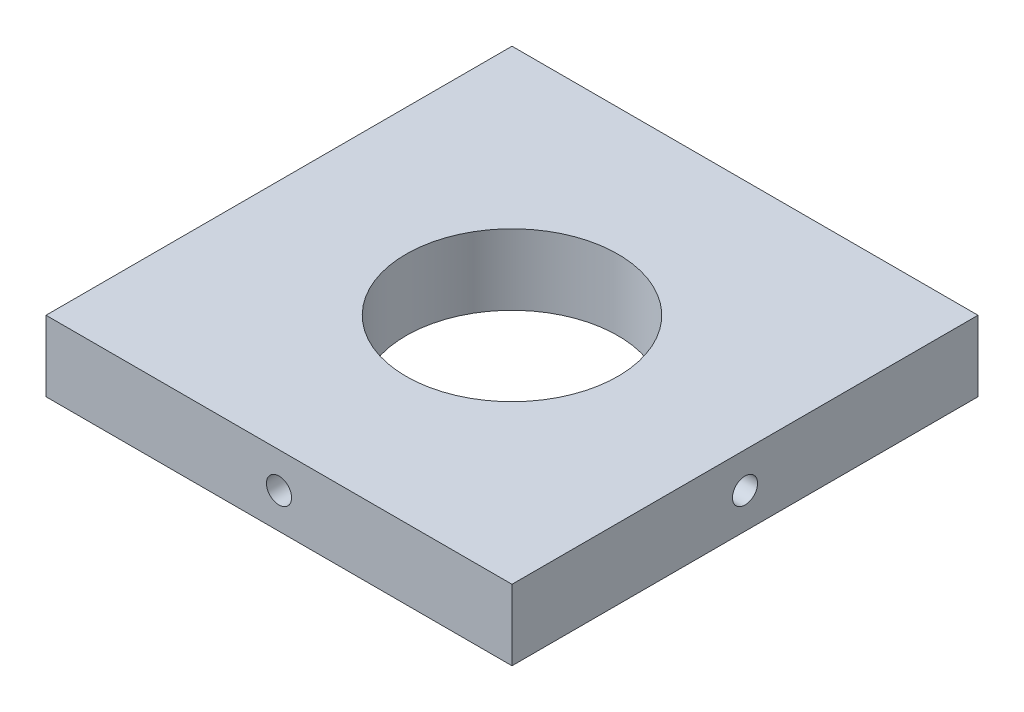
SolidWorks part; units mm, degrees
ref_plane "Front Plane" through (0, 0, 0) normal (0, 0, 1) x (1, 0, 0)
ref_plane "Top Plane" through (0, 0, 0) normal (0, 1, 0) x (1, 0, 0)
ref_plane "Right Plane" through (0, 0, 0) normal (1, 0, 0) x (0, 0, -1)
sketch "Sketch1" plane through (0, 0, 0) normal (0, 1, 0) x (1, 0, 0)
  line L1 (-16.5, -16.5) -> (16.5, -16.5)
  line L2 (-16.5, -16.5) -> (-16.5, 16.5)
  line L3 (-16.5, 16.5) -> (16.5, 16.5)
  line L4 (16.5, -16.5) -> (16.5, 16.5)
  circle A0 centre (0, 0) radius 7.5
extrude "Boss-Extrude1" add sketch "Sketch1" along normal blind 5
sketch "Sketch2" plane through (0, 0, 16.5) normal (0, 0, 1) x (1, 0, 0)
  line L0 (-16.5, 5) -> (16.5, 0)
  line L1 (-16.5, 0) -> (16.5, 5)
  point P8 (0, 0)
hole_wizard "#2-56 Tapped Hole4" positions "Sketch14" profile "Sketch15" tap size "#2-56" standard "ANSI Inch"
sketch "Sketch14" plane through (0, 0, 16.5) normal (0, 0, 1) x (1, 0, 0)
  line L0 (-16.5, 5) -> (16.5, 0) construction
  point P0 (0, 2.5)
sketch "Sketch15" plane through (0, 2.5, 16.5) normal (1, 0, 0) x (0, -1, 0)
  line L0 (0, 0) -> (0, 7)
  line L1 (0, 7) -> (0.889, 6.4658)
  line L2 (0.889, 6.4658) -> (0.889, 0)
  line L5 (0.889, 0) -> (0, 0)
  line L10 (0, 7) -> (-0.889, 6.4658) construction
  line L11 (0, -6.35) -> (0, 107.95) construction
  dimension "Tap Drill Dia." = 1.778
  dimension "Tap Drill Depth" = 7
  dimension "Drill Angle" = 118
cosmetic thread "Hole Thread4"
sketch "Sketch18" plane through (0, 0, -16.5) normal (0, 0, -1) x (-1, 0, 0)
  line L0 (-16.5, 5) -> (16.5, 0)
  line L1 (-16.5, 0) -> (16.5, 5)
hole_wizard "#2-56 Tapped Hole5" positions "Sketch19" profile "Sketch20" tap size "#2-56" standard "ANSI Inch"
sketch "Sketch19" plane through (0, 0, -16.5) normal (0, 0, -1) x (-1, 0, 0)
  line L0 (16.5, 5) -> (-16.5, 0) construction
  point P0 (0, 2.5)
sketch "Sketch20" plane through (0, 2.5, -16.5) normal (1, 0, 0) x (0, 1, 0)
  line L0 (0, 0) -> (0, 8)
  line L1 (0, 8) -> (0.889, 7.4658)
  line L2 (0.889, 7.4658) -> (0.889, 0)
  line L5 (0.889, 0) -> (0, 0)
  line L10 (0, 8) -> (-0.889, 7.4658) construction
  line L11 (0, -6.35) -> (0, 107.95) construction
  dimension "Tap Drill Dia." = 1.778
  dimension "Tap Drill Depth" = 8
  dimension "Drill Angle" = 118
cosmetic thread "Hole Thread5"
sketch "Sketch21" plane through (16.5, 0, 0) normal (1, 0, 0) x (0, 0, -1)
  line L0 (-16.5, 5) -> (16.5, 0)
  line L1 (16.5, 5) -> (-16.5, 0)
  line L2 (-16.5, 0) -> (-16.5, 5) construction
  line L3 (-16.5, 0) -> (16.5, 0) construction
hole_wizard "#2-56 Tapped Hole6" positions "Sketch22" profile "Sketch23" tap size "#2-56" standard "ANSI Inch"
sketch "Sketch22" plane through (16.5, 0, 0) normal (1, 0, 0) x (0, 0, -1)
  line L0 (-16.5, 5) -> (16.5, 0) construction
  point P0 (0, 2.5)
sketch "Sketch23" plane through (16.5, 2.5, 0) normal (0, 1, 0) x (0, 0, -1)
  line L0 (0, 0) -> (0, 8)
  line L1 (0, 8) -> (0.889, 7.4658)
  line L2 (0.889, 7.4658) -> (0.889, 0)
  line L5 (0.889, 0) -> (0, 0)
  line L10 (0, 8) -> (-0.889, 7.4658) construction
  line L11 (0, -6.35) -> (0, 107.95) construction
  dimension "Tap Drill Dia." = 1.778
  dimension "Tap Drill Depth" = 8
  dimension "Drill Angle" = 118
cosmetic thread "Hole Thread6"
sketch "Sketch24" plane through (-16.5, 0, 0) normal (-1, 0, 0) x (0, 0, 1)
  line L0 (-16.5, 5) -> (16.5, 0)
  line L1 (-16.5, 0) -> (16.5, 5)
hole_wizard "#2-56 Tapped Hole7" positions "Sketch25" profile "Sketch26" tap size "#2-56" standard "ANSI Inch"
sketch "Sketch25" plane through (-16.5, 0, 0) normal (-1, 0, 0) x (0, 0, 1)
  line L0 (16.5, 5) -> (-16.5, 0) construction
  point P0 (0, 2.5)
sketch "Sketch26" plane through (-16.5, 2.5, 0) normal (0, 1, 0) x (0, 0, 1)
  line L0 (0, 0) -> (0, 8)
  line L1 (0, 8) -> (0.889, 7.4658)
  line L2 (0.889, 7.4658) -> (0.889, 0)
  line L5 (0.889, 0) -> (0, 0)
  line L10 (0, 8) -> (-0.889, 7.4658) construction
  line L11 (0, -6.35) -> (0, 107.95) construction
  dimension "Tap Drill Dia." = 1.778
  dimension "Tap Drill Depth" = 8
  dimension "Drill Angle" = 118
cosmetic thread "Hole Thread7"
